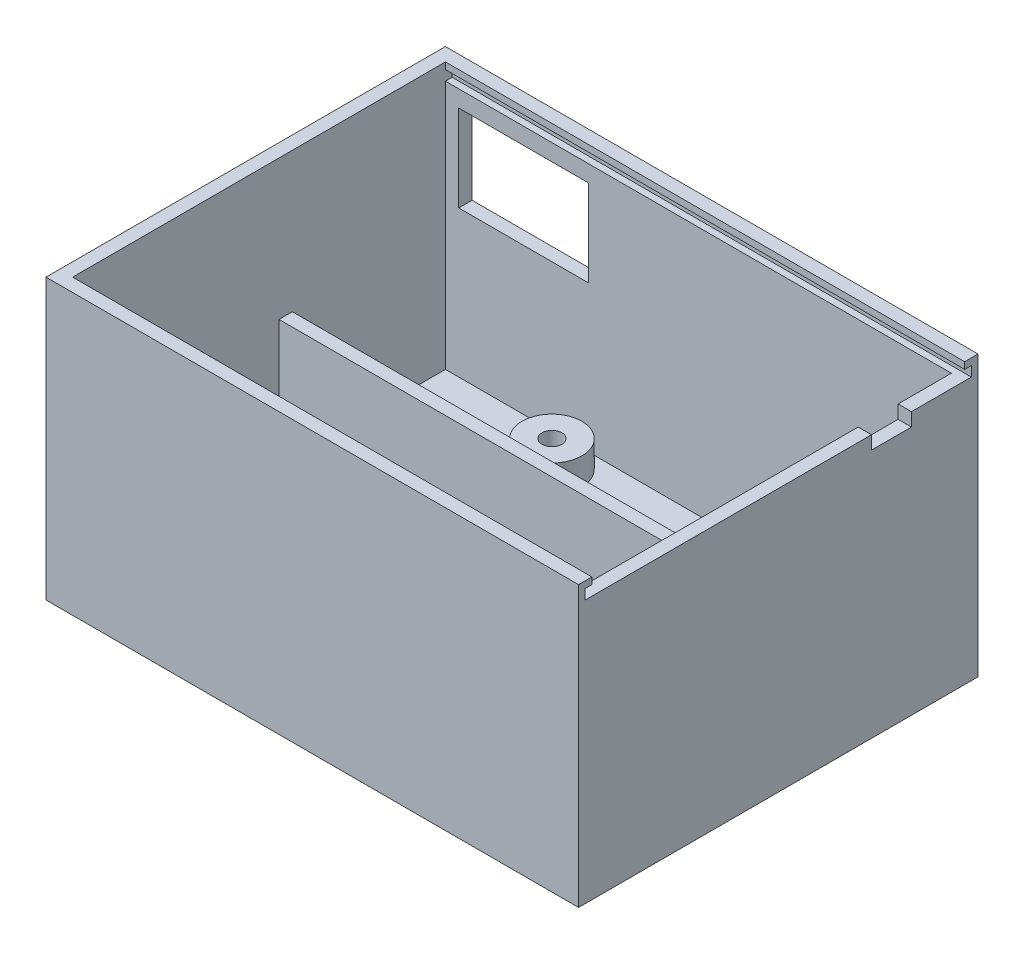
SolidWorks part; units mm, degrees
ref_plane "Ebene vorne" through (0, 0, 0) normal (0, 0, 1) x (1, 0, 0)
ref_plane "Ebene oben" through (0, 0, 0) normal (0, 1, 0) x (1, 0, 0)
ref_plane "Ebene rechts" through (0, 0, 0) normal (1, 0, 0) x (0, 0, -1)
sketch "Skizze1" plane through (0, 0, 0) normal (0, 1, 0) x (1, 0, 0)
  line L1 (0, 0) -> (80, 0)
  line L2 (0, 0) -> (0, 60)
  line L3 (0, 60) -> (80, 60)
  line L4 (80, 0) -> (80, 60)
  dimension "D1" = 60
  dimension "D2" = 80
extrude "Aufsatz-Linear austragen1" add sketch "Skizze1" along normal blind 42
shell "Wandung1" thickness 2
sketch "Skizze2" plane through (0, 2, 0) normal (0, 1, 0) x (1, 0, 0)
  line L0 (78, 2) -> (78, 58) construction
  line L1 (78, 17) -> (18, 17)
  line L2 (78, 17) -> (78, 19)
  line L3 (78, 19) -> (18, 19)
  line L4 (18, 17) -> (18, 19)
  line L5 (2, 2) -> (78, 2) construction
  dimension "D1" = 2
  dimension "D2" = 15
  dimension "D3" = 60
extrude "Aufsatz-Linear austragen2" add sketch "Skizze2" along normal blind 35
sketch "Skizze3" plane through (0, 2, 0) normal (0, 1, 0) x (1, 0, 0)
  line L0 (78, 58) -> (2, 58) construction
  line L1 (2, 58) -> (2, 2) construction
  circle A0 centre (7, 24) radius 1.5
  circle A1 centre (7, 24) radius 4.5
  circle A2 centre (23, 53) radius 1.5
  circle A3 centre (23, 53) radius 4.5
  dimension "D5" = 3
  dimension "D6" = 3
  dimension "D7" = 3
  dimension "D8" = 3
  dimension "D1" = 5
  dimension "D2" = 5
  dimension "D3" = 29
  dimension "D4" = 16
extrude "Aufsatz-Linear austragen3" add sketch "Skizze3" along normal blind 4
sketch "Skizze4" plane through (0, 2, 0) normal (0, 1, 0) x (1, 0, 0)
  line L0 (78, 19) -> (78, 58) construction
  line L1 (18, 19) -> (78, 19) construction
  circle A0 centre (49, 25) radius 1.5
  circle A1 centre (49, 25) radius 4.5
  circle A2 centre (72, 48) radius 1.5
  circle A3 centre (72, 48) radius 4.5
  dimension "D5" = 3
  dimension "D6" = 3
  dimension "D7" = 3
  dimension "D8" = 3
  dimension "D1" = 6
  dimension "D2" = 6
  dimension "D3" = 23
  dimension "D4" = 23
extrude "Aufsatz-Linear austragen4" add sketch "Skizze4" along normal blind 4
sketch "Skizze6" plane through (80, 0, 0) normal (1, 0, 0) x (0, 0, -1)
  line L0 (0, 42) -> (60, 42) construction
  line L1 (2, 42) -> (58, 42)
  line L2 (2, 42) -> (2, 40)
  line L3 (2, 40) -> (58, 40)
  line L4 (58, 42) -> (58, 40)
  line L5 (0, 42) -> (0, 0) construction
  line L6 (60, 42) -> (60, 0) construction
  dimension "D1" = 2
  dimension "D2" = 2
  dimension "D3" = 2
sketch "Skizze7" plane through (80, 0, 0) normal (1, 0, 0) x (0, 0, -1)
  line L1 (1, 39.5) -> (59, 39.5)
  line L2 (1, 39.5) -> (1, 41)
  line L3 (1, 41) -> (59, 41)
  line L4 (59, 39.5) -> (59, 41)
  line L6 (0, 42) -> (60, 42) construction
  line L7 (0, 42) -> (0, 0) construction
  line L8 (60, 42) -> (60, 0) construction
  dimension "D1" = 1.5
  dimension "D2" = 1
  dimension "D3" = 1
  dimension "D4" = 1
extrude "Schnitt-Linear austragen1" cut sketch "Skizze6" against normal up to next
extrude "Schnitt-Linear austragen2" cut sketch "Skizze7" against normal up to surface (78 mm away) up to face at (2, 22, -30)
sketch "Skizze8" plane through (80, 0, 0) normal (1, 0, 0) x (0, 0, -1)
  line L1 (44, 39.5) -> (50, 39.5)
  line L2 (44, 39.5) -> (44, 37.5)
  line L3 (44, 37.5) -> (50, 37.5)
  line L4 (50, 39.5) -> (50, 37.5)
  line L6 (60, 42) -> (60, 0) construction
  line L7 (1, 39.5) -> (59, 39.5) construction
  dimension "D1" = 6
  dimension "D2" = 2
  dimension "D3" = 10
extrude "Schnitt-Linear austragen3" cut sketch "Skizze8" against normal up to next
sketch "Skizze9" plane through (0, 0, -60) normal (0, 0, -1) x (-1, 0, 0)
  line L0 (0, 42) -> (0, 0) construction
  line L1 (-23.5, 37) -> (-4, 37)
  line L2 (-23.5, 37) -> (-23.5, 24)
  line L3 (-23.5, 24) -> (-4, 24)
  line L4 (-4, 37) -> (-4, 24)
  line L5 (-80, 42) -> (0, 42) construction
  dimension "D1" = 4
  dimension "D2" = 19.5
  dimension "D3" = 13
  dimension "D4" = 5
extrude "Schnitt-Linear austragen5" cut sketch "Skizze9" against normal up to next
